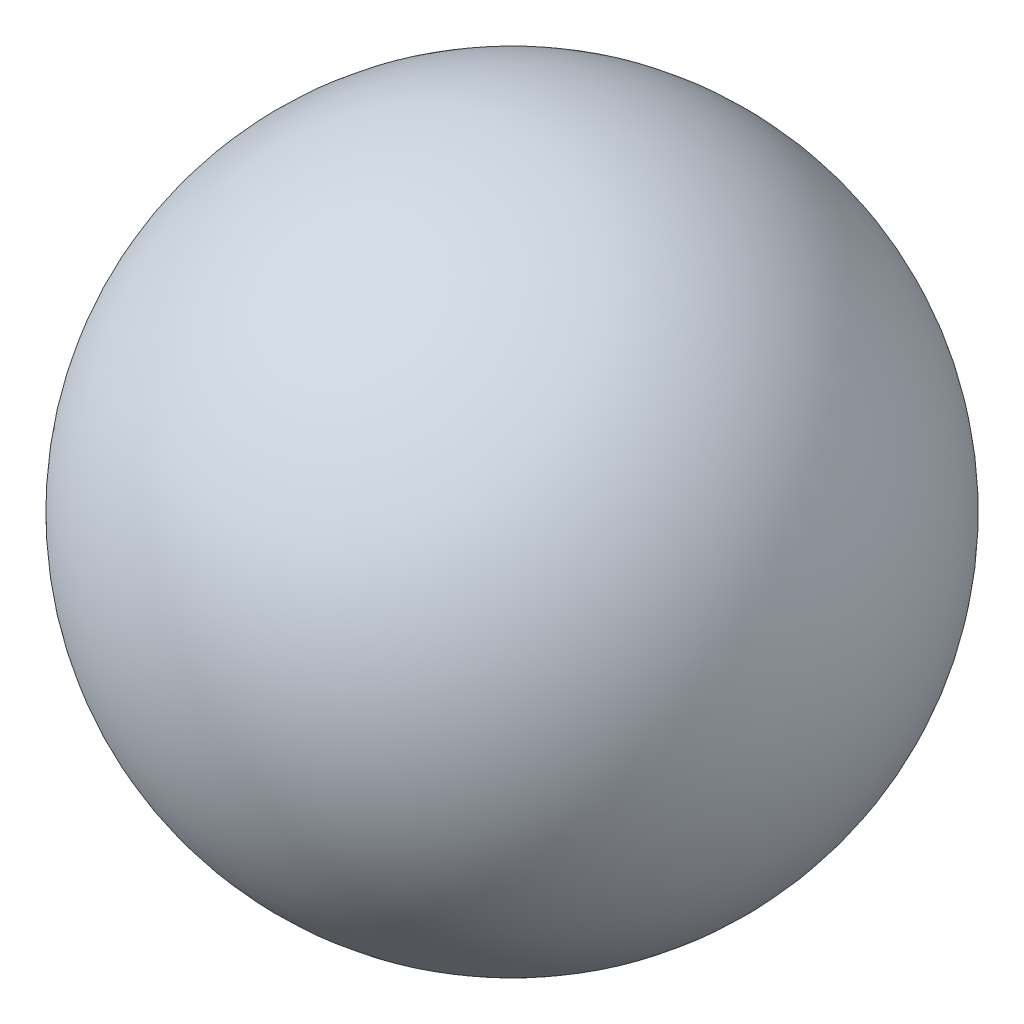
SolidWorks part; units mm, degrees
material "Plain Carbon Steel"
ref_plane "Front Plane" through (0, 0, 0) normal (0, 0, 1) x (1, 0, 0)
ref_plane "Top Plane" through (0, 0, 0) normal (0, 1, 0) x (1, 0, 0)
ref_plane "Right Plane" through (0, 0, 0) normal (1, 0, 0) x (0, 0, -1)
sketch "Sketch1" plane through (0, 0, 0) normal (0, 0, 1) x (1, 0, 0)
  line L0 (0, 0.5) -> (0, -0.5)
  arc A0 (0, 0.5) -> (0, -0.5) centre (0, 0) ccw
  dimension "D1" = 1
revolve "Revolve1" add sketch "Sketch1" angle 360 about L0
